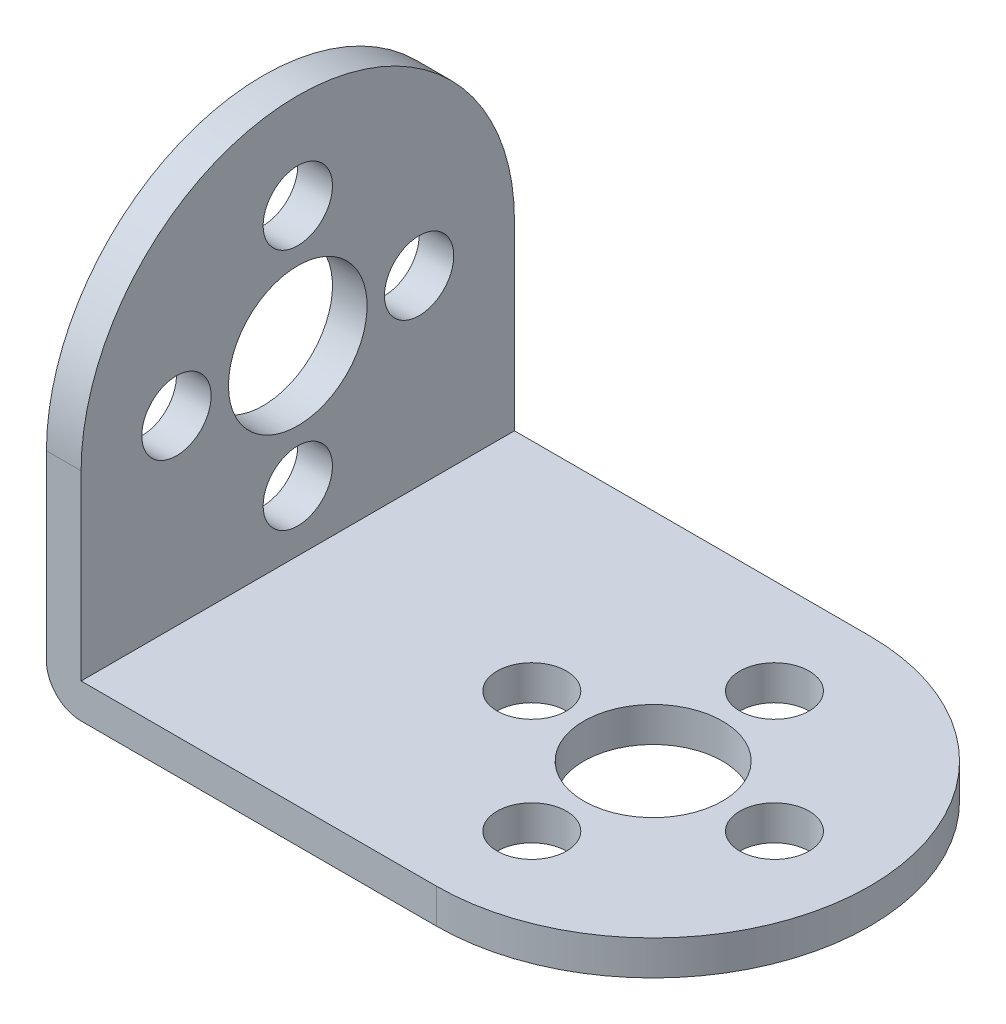
SolidWorks part; units mm, degrees
material "可锻铸铁"
ref_plane "前视基准面" through (0, 0, 0) normal (0, 0, 1) x (1, 0, 0)
ref_plane "上视基准面" through (0, 0, 0) normal (0, 1, 0) x (1, 0, 0)
ref_plane "右视基准面" through (0, 0, 0) normal (1, 0, 0) x (0, 0, -1)
sketch "草图1" plane through (0, 0, 0) normal (0, 1, 0) x (1, 0, 0)
  line L1 (-11.25, 12.5) -> (11.25, 12.5)
  line L2 (-11.25, 12.5) -> (-11.25, -12.5)
  line L3 (-11.25, -12.5) -> (11.25, -12.5)
  arc A0 (11.25, -12.5) -> (11.25, 12.5) centre (11.25, 0) ccw
  circle A1 centre (11.25, 0) radius 4
  circle A2 centre (18.25, 0) radius 2
  circle A3 centre (11.25, -7) radius 2
  circle A4 centre (4.25, 0) radius 2
  circle A5 centre (11.25, 7) radius 2
  point P0 (0, 0)
  dimension "D2" = 22.5
  dimension "D3" = 8
  dimension "D4" = 4
  dimension "D1" = 25
  dimension "D5" = 7
  dimension "D6" = 12.5
  dimension "D7" = 4
extrude "凸台-拉伸1" add sketch "草图1" along normal blind 2
ref_plane "基准面4" through (0, 2, 0) normal (0, 1, 0) x (1, 0, 0)
sketch "草图2" plane through (-11.25, 0, 0) normal (-1, 0, 0) x (0, 0, 1)
  line L1 (-12.5, 0) -> (12.5, 0)
  line L2 (-12.5, 0) -> (-12.5, 12.5)
  line L4 (12.5, 0) -> (12.5, 12.5)
  arc A0 (12.5, 12.5) -> (-12.5, 12.5) centre (0, 12.5) ccw
  circle A1 centre (0, 12.5) radius 4
  circle A2 centre (0, 19.5) radius 2
  circle A3 centre (7, 12.5) radius 2
  circle A4 centre (0, 5.5) radius 2
  circle A5 centre (-7, 12.5) radius 2
  dimension "D3" = 8
  dimension "D4" = 4
  dimension "D1" = 25
  dimension "D2" = 12.5
  dimension "D5" = 7
  dimension "D6" = 12.5
  dimension "D7" = 12.5
  dimension "D8" = 4
extrude "凸台-拉伸2" add sketch "草图2" against normal blind 2
fillet "圆角1" radius 2 1 edges at (-11.25, 0, 0)
